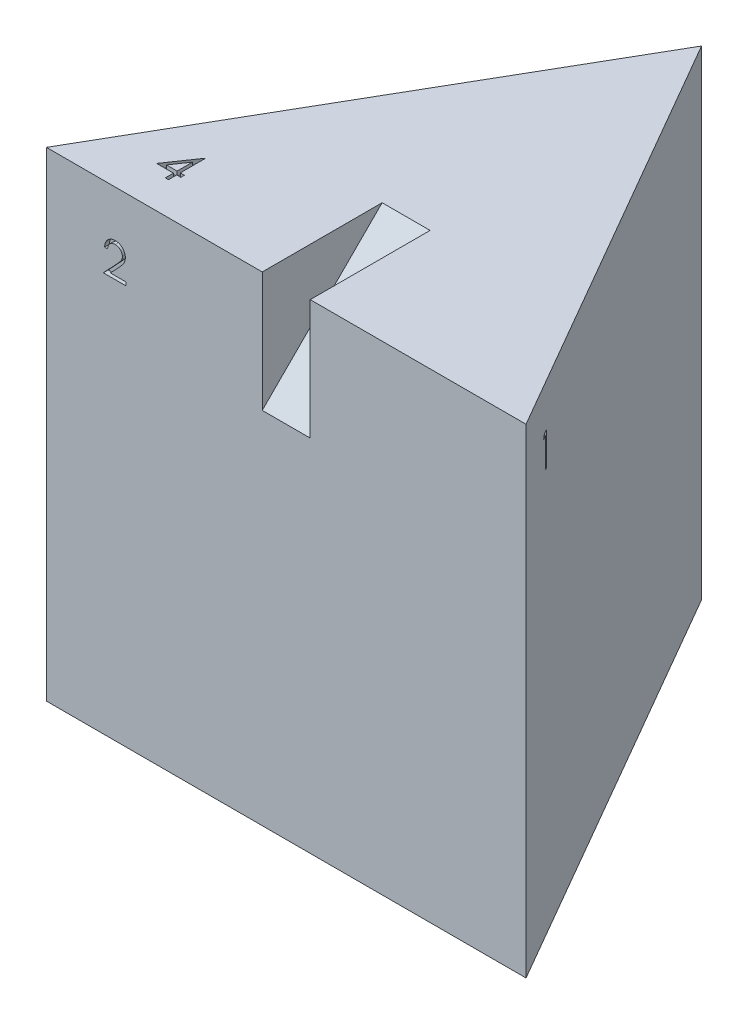
SolidWorks part; units mm, degrees
ref_plane "Front Plane" through (0, 0, 0) normal (0, 0, 1) x (1, 0, 0)
ref_plane "Top Plane" through (0, 0, 0) normal (0, 1, 0) x (1, 0, 0)
ref_plane "Right Plane" through (0, 0, 0) normal (1, 0, 0) x (0, 0, -1)
sketch "Sketch1" plane through (0, 0, 0) normal (0, 1, 0) x (1, 0, 0)
  line L0 (0, 0) -> (-50, -86.6025)
  line L1 (-50, -86.6025) -> (50, -86.6025)
  line L2 (50, -86.6025) -> (0, 0)
  dimension "D1" = 100
extrude "Boss-Extrude1" add sketch "Sketch1" along normal blind 100
sketch "Sketch2" plane through (0, 0, 0) normal (1, 0, 0) x (0, 0, -1)
  line L0 (-86.6025, 100) -> (-61.6025, 100)
  line L1 (-86.6025, 100) -> (0, 100) construction
  line L2 (-61.6025, 100) -> (-86.6025, 75)
  line L3 (-86.6025, 100) -> (-86.6025, 0) construction
  line L4 (-86.6025, 75) -> (-86.6025, 100)
  dimension "D1" = 25
extrude "Cut-Extrude1" cut sketch "Sketch2" against normal mid plane 10
sketch "Sketch3" plane through (0, 0, 0) normal (0.866, 0, -0.5) x (-0.5, 0, -0.866)
  text T0 "1" font "Century Gothic" height in points 26
extrude "Cut-Extrude2" cut sketch "Sketch3" against normal blind 1
sketch "Sketch4" plane through (0, 0, 86.6025) normal (0, 0, 1) x (1, 0, 0)
  text T0 "2" font "Century Gothic" height in points 26
extrude "Cut-Extrude3" cut sketch "Sketch4" against normal blind 1
sketch "Sketch5" plane through (0, 0, 0) normal (-0.866, 0, -0.5) x (-0.5, 0, 0.866)
  text T0 "3" font "Century Gothic" height in points 26
extrude "Cut-Extrude4" cut sketch "Sketch5" against normal blind 1
sketch "Sketch6" plane through (0, 100, 0) normal (0, 1, 0) x (1, 0, 0)
  text T0 "4" font "Century Gothic" height in points 28
extrude "Cut-Extrude5" cut sketch "Sketch6" against normal blind 1
